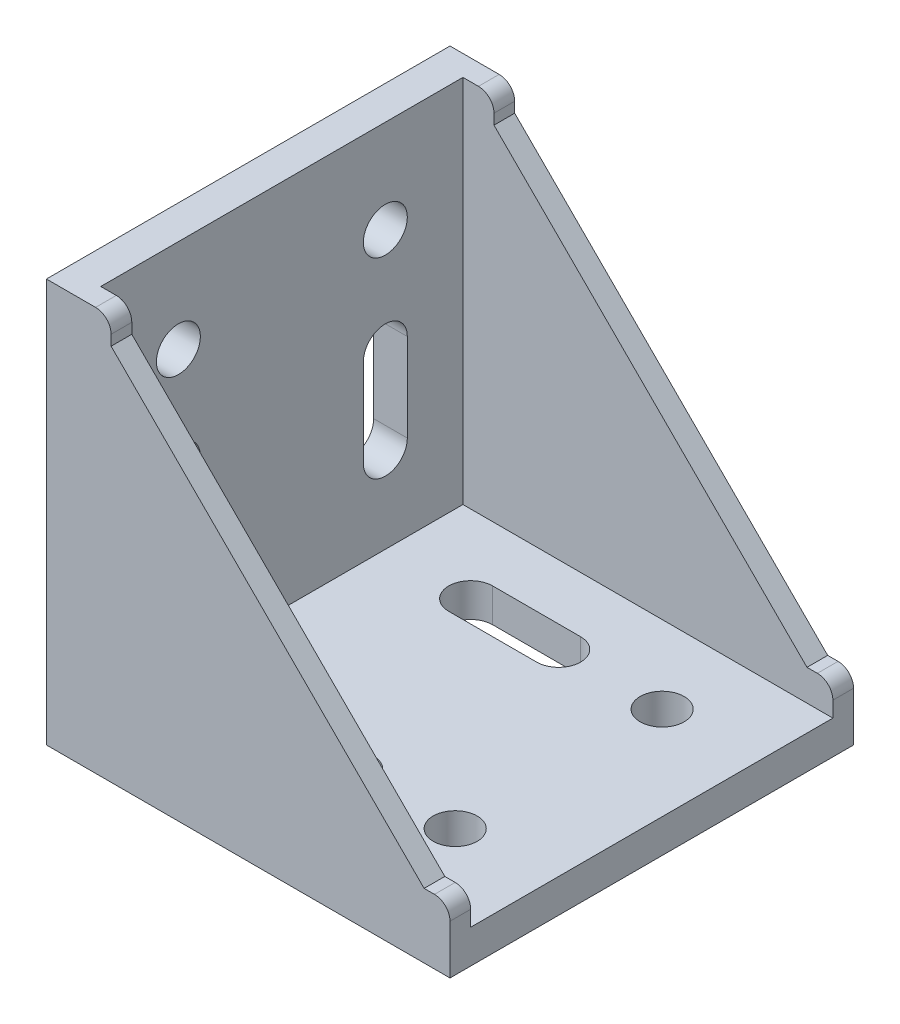
SolidWorks part; units mm, degrees
material "Алюминиевый сплав"
ref_plane "Спереди" through (0, 0, 0) normal (0, 0, 1) x (1, 0, 0)
ref_plane "Сверху" through (0, 0, 0) normal (0, 1, 0) x (1, 0, 0)
ref_plane "Справа" through (0, 0, 0) normal (1, 0, 0) x (0, 0, -1)
sketch "Эскиз1" plane through (0, 0, 0) normal (0, 0, 1) x (1, 0, 0)
  line L0 (0, 78) -> (0, 0)
  line L1 (0, 0) -> (78, 0)
  line L2 (78, 0) -> (78, 6.5)
  line L4 (6.5, 78) -> (0, 78)
  line L5 (6.5, 78) -> (6.5, 6.5)
  line L6 (6.5, 6.5) -> (78, 6.5)
  dimension "D1" = 78
  dimension "D2" = 6.5
extrude "Бобышка-Вытянуть1" add sketch "Эскиз1" along normal mid plane 78
sketch "Эскиз2" plane through (0, 0, 39) normal (0, 0, 1) x (1, 0, 0)
  line L1 (78, 6.5) -> (6.5, 6.5)
  line L2 (6.5, 6.5) -> (6.5, 78)
  line L3 (6.5, 78) -> (9.5, 78)
  line L4 (12.5, 75) -> (12.5, 73)
  line L5 (12.5, 73) -> (73, 12.5)
  line L6 (73, 12.5) -> (75, 12.5)
  line L7 (78, 9.5) -> (78, 6.5)
  arc A0 (75, 12.5) -> (78, 9.5) centre (75, 9.5) cw
  arc A1 (9.5, 78) -> (12.5, 75) centre (9.5, 75) cw
  point P16 (12.5, 78)
  dimension "D2" = 3
  dimension "D1" = 5
  dimension "D3" = 6
extrude "Бобышка-Вытянуть2" add sketch "Эскиз2" against normal blind 4
mirror "Зеркальное отражение2" about plane through (0, 0, 0) normal (0, 0, 1) of "Бобышка-Вытянуть2"
sketch "Эскиз3" plane through (0, 6.5, 0) normal (0, 1, 0) x (1, 0, 0)
  line L0 (23, -20) -> (40, -20) construction
  line L1 (23, -15.75) -> (40, -15.75)
  line L2 (23, -24.25) -> (40, -24.25)
  line L5 (78, -35) -> (78, 35) construction
  line L6 (0, 0) -> (78, 0) construction
  line L7 (23, 20) -> (40, 20) construction
  line L8 (23, 15.75) -> (40, 15.75)
  line L9 (23, 24.25) -> (40, 24.25)
  arc A0 (23, -15.75) -> (23, -24.25) centre (23, -20) ccw
  arc A1 (40, -24.25) -> (40, -15.75) centre (40, -20) ccw
  circle A2 centre (60, -20) radius 4.25
  arc A3 (23, 15.75) -> (23, 24.25) centre (23, 20) cw
  arc A4 (40, 24.25) -> (40, 15.75) centre (40, 20) cw
  circle A5 centre (60, 20) radius 4.25
  point P2 (31.5, -20)
  point P17 (31.5, 20)
  dimension "D2" = 4.25
  dimension "D3" = 18
  dimension "D4" = 20
  dimension "D5" = 40
  dimension "D1" = 17
extrude "Вырез-Вытянуть1" cut sketch "Эскиз3" against normal through all
sketch "Эскиз4" plane through (0, 0, 0) normal (0, -1, 0) x (1, 0, 0)
  line L0 (0, 39) -> (0, -39) construction
  line L1 (3, -24) -> (6, -24)
  line L2 (3, -24) -> (3, -16)
  line L3 (3, -16) -> (6, -16)
  line L4 (6, -24) -> (6, -16)
  line L5 (3, -24) -> (6, -16) construction
  line L6 (3, -16) -> (6, -24) construction
  line L7 (72, -24) -> (75, -24)
  line L8 (72, -24) -> (72, -16)
  line L9 (72, -16) -> (75, -16)
  line L10 (75, -24) -> (75, -16)
  line L11 (72, -24) -> (75, -16) construction
  line L12 (72, -16) -> (75, -24) construction
  line L13 (78, 39) -> (78, -39) construction
  line L14 (0, 0) -> (78, 0) construction
  line L15 (72, 16) -> (75, 24) construction
  line L16 (72, 24) -> (75, 16) construction
  line L17 (3, 16) -> (6, 24) construction
  line L18 (3, 24) -> (6, 16) construction
  line L19 (75, 24) -> (75, 16)
  line L20 (72, 16) -> (75, 16)
  line L21 (72, 24) -> (72, 16)
  line L22 (72, 24) -> (75, 24)
  line L23 (6, 24) -> (6, 16)
  line L24 (3, 16) -> (6, 16)
  line L25 (3, 24) -> (3, 16)
  line L26 (3, 24) -> (6, 24)
  point P0 (4.5, -20)
  point P5 (73.5, -20)
  point P25 (73.5, 20)
  point P26 (4.5, 20)
  dimension "D1" = 3
  dimension "D2" = 3
  dimension "D3" = 8
  dimension "D4" = 3
  dimension "D5" = 40
extrude "Бобышка-Вытянуть3" add sketch "Эскиз4" along normal blind 2.5
ref_plane "Плоскость1" through (0, 0, 0) normal (-0.7071, 0.7071, 0) x (0.7071, 0.7071, 0)
mirror "Зеркальное отражение3" about plane through (0, 0, 0) normal (-0.7071, 0.7071, 0) of "Бобышка-Вытянуть3", "Вырез-Вытянуть1"
